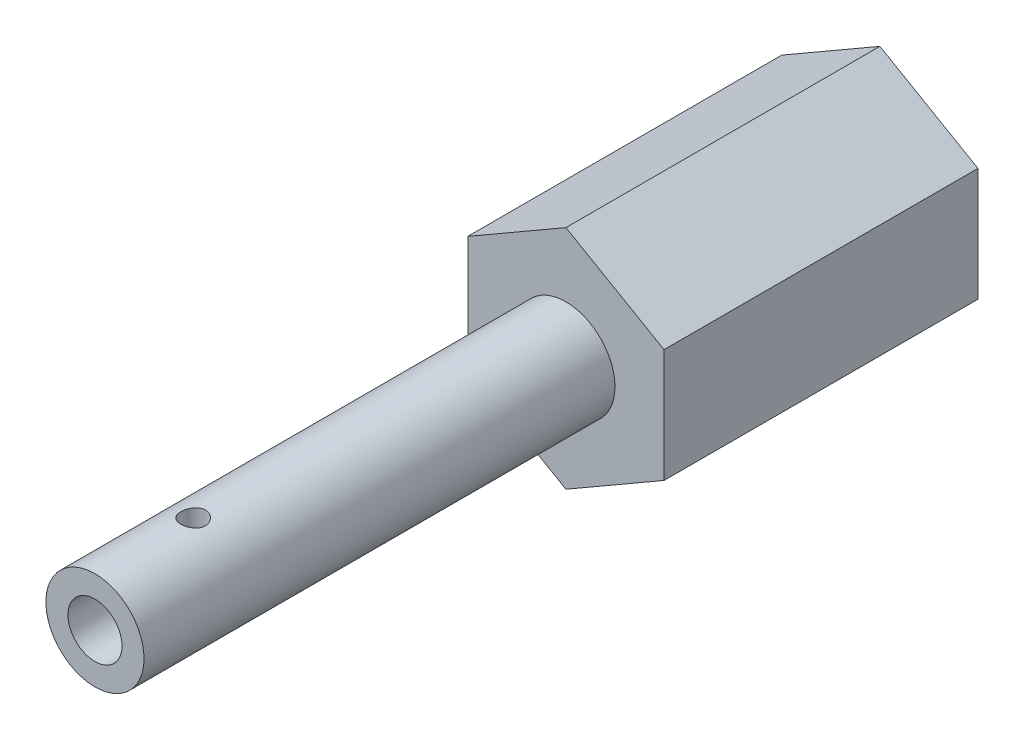
SolidWorks part; units mm, degrees
ref_plane "Front Plane" through (0, 0, 0) normal (0, 0, 1) x (1, 0, 0)
ref_plane "Top Plane" through (0, 0, 0) normal (0, 1, 0) x (1, 0, 0)
ref_plane "Right Plane" through (0, 0, 0) normal (1, 0, 0) x (0, 0, -1)
sketch "Sketch1" plane through (0, 0, 0) normal (0, 0, 1) x (1, 0, 0)
  line L1 (0, 7.3323) -> (-6.35, 3.6662)
  line L2 (-6.35, 3.6662) -> (-6.35, -3.6662)
  line L3 (-6.35, -3.6662) -> (0, -7.3323)
  line L4 (0, -7.3323) -> (6.35, -3.6662)
  line L5 (6.35, -3.6662) -> (6.35, 3.6662)
  line L6 (6.35, 3.6662) -> (0, 7.3323)
  circle A0 centre (0, 0) radius 6.35 construction
  dimension "D1" = 12.7
extrude "Boss-Extrude1" add sketch "Sketch1" along normal blind 20.32 contours L6 L1 L2 L3 L4 L5
sketch "Sketch2" plane through (0, 0, 20.32) normal (0, 0, 1) x (1, 0, 0)
  circle A0 centre (0, 0) radius 3.175
  dimension "D1" = 6.35
extrude "Boss-Extrude2" add sketch "Sketch2" along normal blind 30.48
hole_wizard "Ø3.5 (3.5) Diameter Hole1" positions "Sketch3" profile "Sketch4" hole size "Ø3.5" standard "ANSI Metric"
sketch "Sketch3" plane through (0, 0, 50.8) normal (0, 0, 1) x (1, 0, 0)
  point P0 (0, 0)
sketch "Sketch4" plane through (0, 0, 50.8) normal (1, 0, 0) x (0, -1, 0)
  line L0 (0, 0) -> (0, 26.4515)
  line L1 (0, 26.4515) -> (1.75, 25.4)
  line L2 (1.75, 25.4) -> (1.75, 0)
  line L5 (1.75, 0) -> (0, 0)
  line L10 (0, 26.4515) -> (-1.75, 25.4) construction
  line L11 (0, -6.35) -> (0, 107.95) construction
  dimension "Hole Dia." = 3.5
  dimension "Hole Depth" = 25.4
  dimension "Drill Angle" = 118
ref_plane "Plane1" through (0, 7.62, 0) normal (0, 1, 0) x (1, 0, 0)
hole_wizard "1/16 (0.0625) Diameter Hole1" positions "Sketch5" profile "Sketch6" hole size "1/16" standard "ANSI Inch" end condition through all
sketch "Sketch5" plane through (0, 7.62, 0) normal (0, 1, 0) x (1, 0, 0)
  line L0 (-3.175, -50.8) -> (3.175, -50.8) construction
  point P0 (0, -44.45)
  dimension "D1" = 6.35
sketch "Sketch6" plane through (0, 7.62, 44.45) normal (1, 0, 0) x (0, 0, 1)
  line L0 (0, 0) -> (0, 14.9523)
  line L1 (0, 14.9523) -> (0.7937, 14.9523)
  line L2 (0.7937, 14.9523) -> (0.7937, 0)
  line L5 (0.7937, 0) -> (0, 0)
  line L11 (0, -6.35) -> (0, 107.95) construction
  dimension "Thru Hole Dia." = 1.5875
  dimension "Thru Hole Depth" = 14.9523
